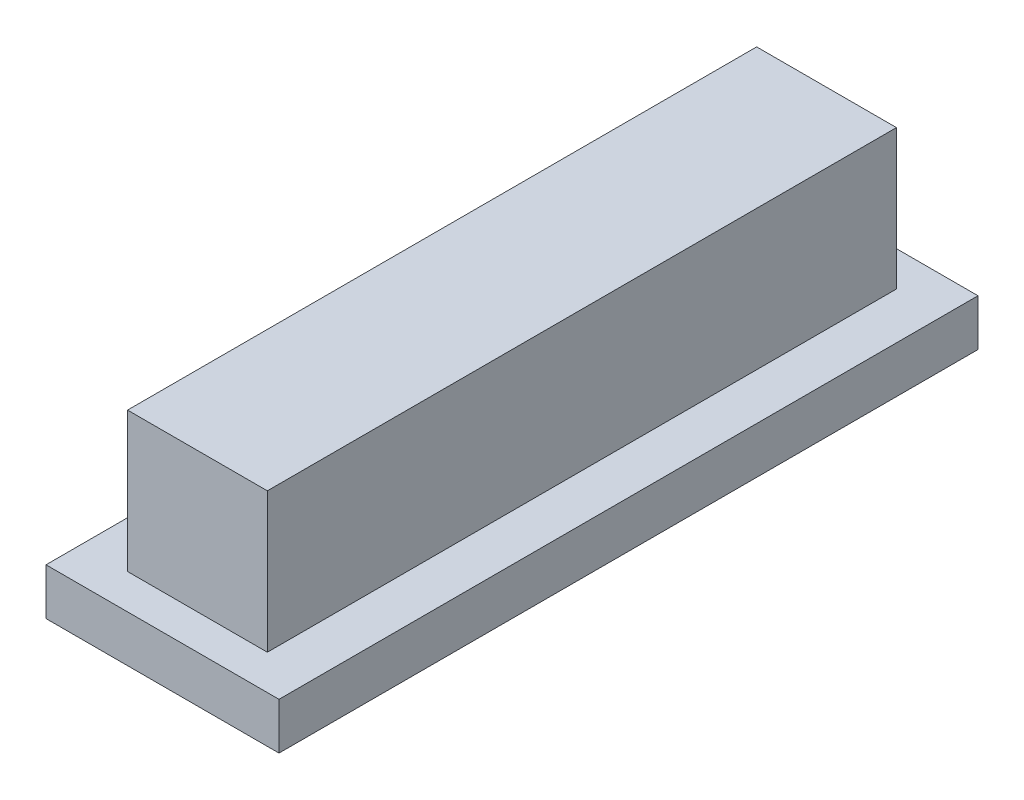
SolidWorks part; units mm, degrees
ref_plane "前视基准面" through (0, 0, 0) normal (0, 0, 1) x (1, 0, 0)
ref_plane "上视基准面" through (0, 0, 0) normal (0, 1, 0) x (1, 0, 0)
ref_plane "右视基准面" through (0, 0, 0) normal (1, 0, 0) x (0, 0, -1)
sketch "草图1" plane through (0, 0, 0) normal (0, 1, 0) x (1, 0, 0)
  line L1 (1.5, -11.1) -> (-1.5, -11.1)
  line L2 (1.5, -11.1) -> (1.5, 11.1)
  line L3 (1.5, 11.1) -> (-1.5, 11.1)
  line L4 (-1.5, -11.1) -> (-1.5, 11.1)
  line L5 (1.5, -11.1) -> (-1.5, 11.1) construction
  line L6 (1.5, 11.1) -> (-1.5, -11.1) construction
  line L7 (-3, -13.5) -> (3, -13.5)
  line L8 (-3, -13.5) -> (-3, 13.5)
  line L9 (-3, 13.5) -> (3, 13.5)
  line L10 (3, -13.5) -> (3, 13.5)
  line L11 (-3, -13.5) -> (3, 13.5) construction
  line L12 (-3, 13.5) -> (3, -13.5) construction
  point P0 (0, 0)
  point P6 (0, 0)
  dimension "D1" = 22.2
  dimension "D2" = 3
  dimension "D3" = 27
  dimension "D4" = 6
extrude "凸台-拉伸1" add sketch "草图1" along normal blind 4
sketch "草图2" plane through (0, 4, 0) normal (0, 1, 0) x (1, 0, 0)
  line L1 (-3, -13.5) -> (3, -13.5)
  line L2 (-3, -13.5) -> (-3, 13.5)
  line L3 (-3, 13.5) -> (3, 13.5)
  line L4 (3, -13.5) -> (3, 13.5)
extrude "凸台-拉伸2" add sketch "草图2" along normal blind 2
sketch "草图3" plane through (0, 0, 0) normal (0, -1, 0) x (1, 0, 0)
  line L1 (-5, -15) -> (5, -15)
  line L2 (-5, -15) -> (-5, 15)
  line L3 (-5, 15) -> (5, 15)
  line L4 (5, -15) -> (5, 15)
  line L5 (-5, -15) -> (5, 15) construction
  line L6 (-5, 15) -> (5, -15) construction
  point P0 (0, 0)
  dimension "D1" = 30
  dimension "D2" = 10
extrude "凸台-拉伸3" add sketch "草图3" along normal blind 2
sketch "草图4" plane through (0, -2, 0) normal (0, -1, 0) x (1, 0, 0)
  line L1 (2.95, 12.5) -> (-2.95, 12.5)
  line L2 (2.95, 12.5) -> (2.95, -12.5)
  line L3 (2.95, -12.5) -> (-2.95, -12.5)
  line L4 (-2.95, 12.5) -> (-2.95, -12.5)
  line L5 (2.95, 12.5) -> (-2.95, -12.5) construction
  line L6 (2.95, -12.5) -> (-2.95, 12.5) construction
  point P0 (0, 0)
  dimension "D1" = 25
  dimension "D2" = 5.9
extrude "切除-拉伸3" cut sketch "草图4" against normal blind 2
